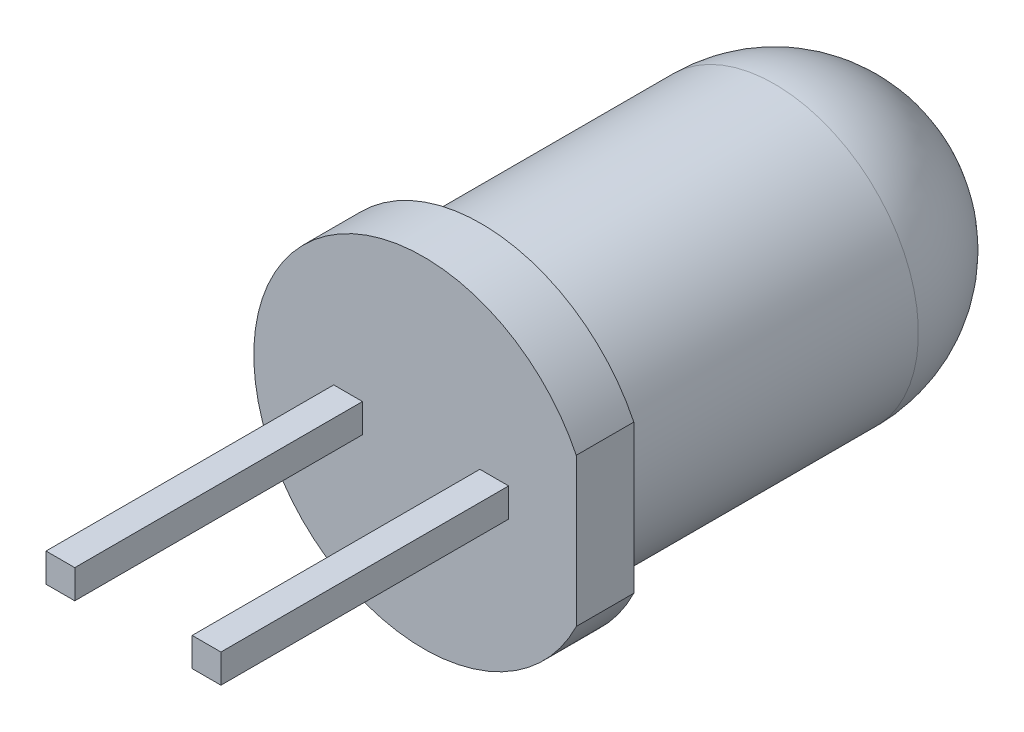
SolidWorks part; units mm, degrees
ref_plane "Front Plane" through (0, 0, 0) normal (0, 0, 1) x (1, 0, 0)
ref_plane "Top Plane" through (0, 0, 0) normal (0, 1, 0) x (1, 0, 0)
ref_plane "Right Plane" through (0, 0, 0) normal (1, 0, 0) x (0, 0, -1)
sketch "Sketch1" plane through (0, 0, 0) normal (0, 1, 0) x (1, 0, 0)
  line L0 (0.0414, -1.3187) -> (-2.9086, -1.3187)
  line L1 (-2.9086, -1.3187) -> (-2.9086, -0.3187)
  line L2 (-2.9086, -0.3187) -> (-2.4586, -0.3187)
  line L3 (-2.4586, -0.3187) -> (-2.4586, 4.7813)
  line L4 (0.0414, 7.2813) -> (0.0414, -1.3187) construction
  line L5 (0.0414, 7.2813) -> (-4.1738, 7.2812) construction
  line L6 (-0.2586, 6.9607) -> (0.0414, 6.9607)
  line L7 (-0.2586, -1.0187) -> (0.0414, -1.0187)
  line L8 (-0.2586, -1.0187) -> (-2.6086, -1.0187)
  line L9 (-2.6086, -1.0187) -> (-2.6086, -0.6187)
  line L10 (-2.6086, -0.6187) -> (-2.1586, -0.6187)
  line L11 (-2.1586, -0.6187) -> (-2.1586, 4.7813)
  line L12 (-0.2586, 6.9607) -> (-0.2586, -1.0187) construction
  line L13 (0.0414, 7.2813) -> (0.0414, -1.3187) construction
  line L14 (0.0414, 7.2813) -> (0.0414, 6.9607)
  line L15 (0.0414, -1.0187) -> (0.0414, -1.3187)
  line L16 (0.0414, -1.3187) -> (0.04, -1.314)
  arc A0 (-2.4586, 4.7813) -> (0.0414, 7.2813) centre (0.0414, 4.7813) cw
  arc A1 (-2.1586, 4.7813) -> (-0.2586, 6.9607) centre (0.0414, 4.7813) cw
  dimension "D1" = 8.6
  dimension "D2" = 2.5
  dimension "D3" = 2.95
  dimension "D4" = 1
  dimension "D5" = 0.3
revolve "Revolve3" add sketch "Sketch1" angle 360 about L4
sketch "Sketch2" plane through (0, 0, 1.3187) normal (0, 0, 1) x (1, 0, 0)
  line L0 (1.52, 0.2398) -> (1.02, 0.2398)
  line L1 (-1.02, 0.2398) -> (-1.52, 0.2398)
  line L2 (-1.02, 0.2398) -> (-1.02, -0.2602)
  line L3 (-1.02, -0.2602) -> (-1.52, -0.2602)
  line L4 (-1.52, 0.2398) -> (-1.52, -0.2602)
  line L5 (1.52, 0.2398) -> (1.52, -0.2602)
  line L6 (1.52, -0.2602) -> (1.02, -0.2602)
  line L7 (1.02, 0.2398) -> (1.02, -0.2602)
  point P4 (-1.27, 0.2398)
  point P5 (1.27, 0.2398)
  point P10 (1.27, -0.2602)
  dimension "D1" = 0.5
  dimension "D2" = 0.5
  dimension "D4" = 2.54
  dimension "D5" = 1.27
  dimension "D3" = 2
extrude "Boss-Extrude1" add sketch "Sketch2" along normal blind 5
sketch "Sketch3" plane through (0.0201, 0, 1.3187) normal (0, 0, 1) x (1, 0, 0)
  line L0 (2.6752, 2.1927) -> (2.6752, -2.2689)
  line L1 (2.6752, -2.2689) -> (4.2948, -2.5024)
  line L2 (4.2948, -2.5024) -> (4.1605, 2.2994)
  line L3 (4.1605, 2.2994) -> (2.6752, 2.1927)
extrude "Cut-Extrude1" cut sketch "Sketch3" against normal up to next
